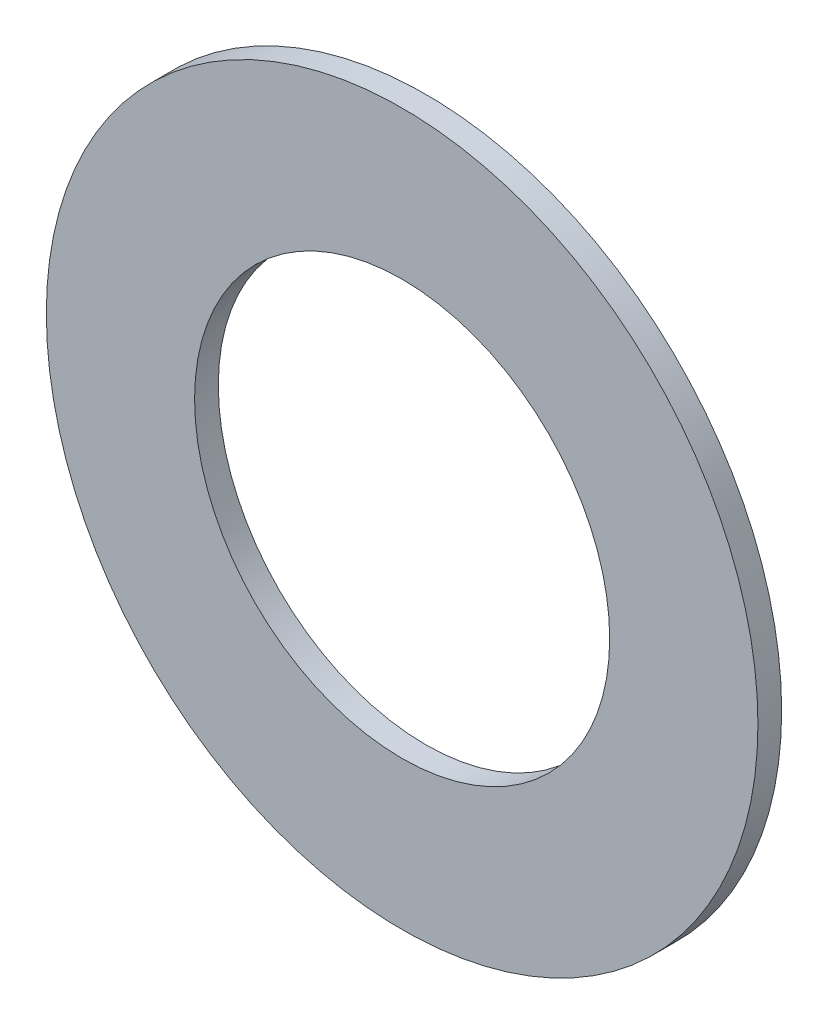
SolidWorks part; units mm, degrees
ref_plane "前视基准面" through (0, 0, 0) normal (0, 0, 1) x (1, 0, 0)
ref_plane "上视基准面" through (0, 0, 0) normal (0, 1, 0) x (1, 0, 0)
ref_plane "右视基准面" through (0, 0, 0) normal (1, 0, 0) x (0, 0, -1)
other "Configuration Table"
sketch "草图1" plane through (0, 0, 0) normal (0, 0, 1) x (1, 0, 0)
  circle A0 centre (0, 0) radius 8.75
  circle A1 centre (0, 0) radius 15
  dimension "D1" = 17.5
  dimension "D2" = 30
extrude "凸台-拉伸1" add sketch "草图1" along normal blind 1
